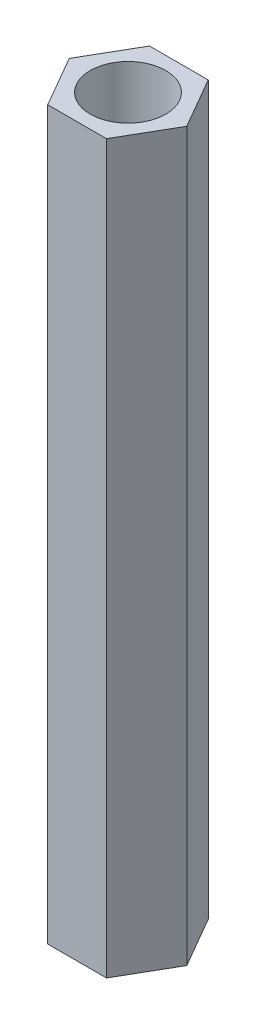
SolidWorks part; units mm, degrees
material "黄铜"
ref_plane "前视基准面" through (0, 0, 0) normal (0, 0, 1) x (1, 0, 0)
ref_plane "上视基准面" through (0, 0, 0) normal (0, 1, 0) x (1, 0, 0)
ref_plane "右视基准面" through (0, 0, 0) normal (1, 0, 0) x (0, 0, -1)
sketch "草图1" plane through (0, 0, 0) normal (0, 1, 0) x (1, 0, 0)
  line L1 (4.0415, 0) -> (2.0207, 3.5)
  line L2 (2.0207, 3.5) -> (-2.0207, 3.5)
  line L3 (-2.0207, 3.5) -> (-4.0415, 0)
  line L4 (-4.0415, 0) -> (-2.0207, -3.5)
  line L5 (-2.0207, -3.5) -> (2.0207, -3.5)
  line L6 (2.0207, -3.5) -> (4.0415, 0)
  circle A0 centre (0, 0) radius 3.5 construction
  dimension "D1" = 7
extrude "凸台-拉伸1" add sketch "草图1" along normal blind 50
sketch "草图2" plane through (0, 50, 0) normal (0, 1, 0) x (1, 0, 0)
  circle A0 centre (0, 0) radius 2.6
  dimension "D1" = 5.2
extrude "切除-拉伸1" cut sketch "草图2" against normal through all
ref_plane "基准面1" through (0, 10, 0) normal (0, -1, 0) x (-1, 0, 0)
sketch "草图3" plane through (0, 10, 0) normal (0, -1, 0) x (-1, 0, 0)
  circle A0 centre (0, 0) radius 2.6 construction
  circle A1 centre (0, 0) radius 2.6
extrude "凸台-拉伸2" add sketch "草图3" against normal offset from surface (30 mm away) 10 up to face at (0, 50, 2.6)
